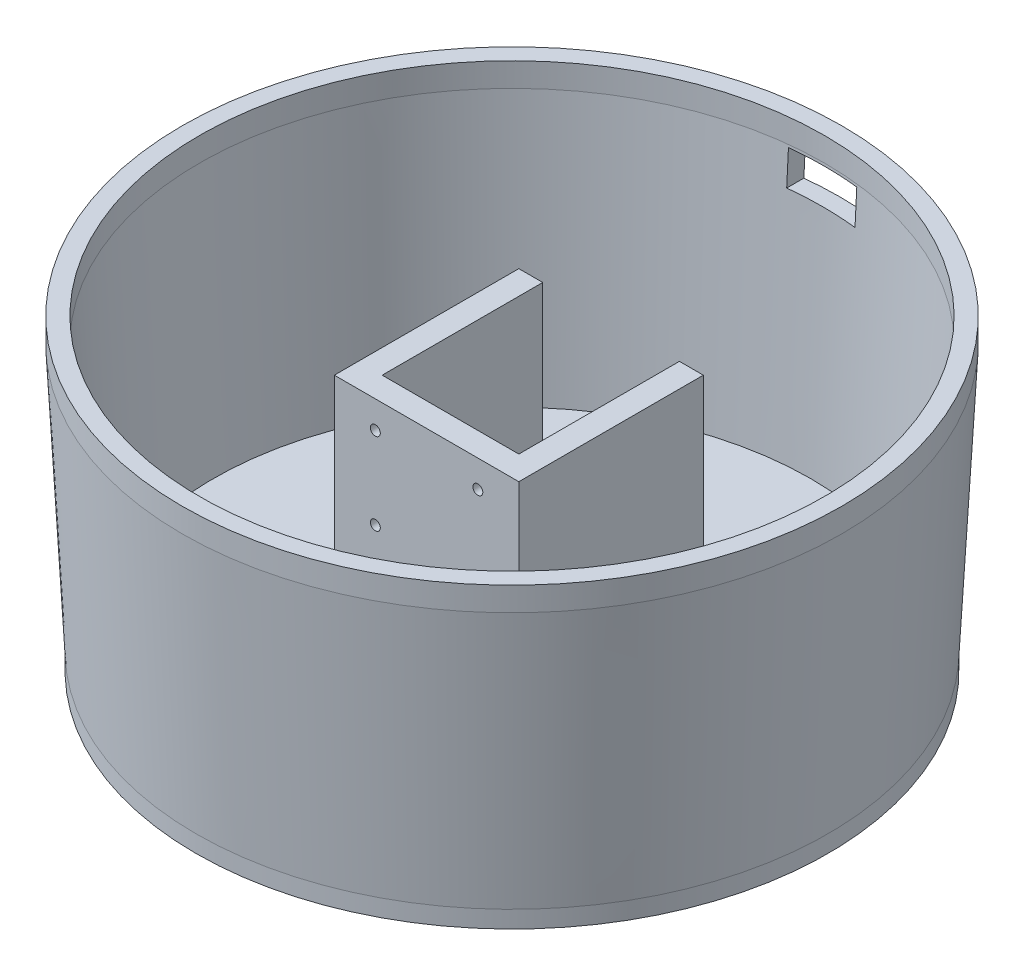
SolidWorks part; units mm, degrees
ref_plane "정면" through (0, 0, 0) normal (0, 0, 1) x (1, 0, 0)
ref_plane "윗면" through (0, 0, 0) normal (0, 1, 0) x (1, 0, 0)
ref_plane "우측면" through (0, 0, 0) normal (1, 0, 0) x (0, 0, -1)
sketch "스케치1" plane through (0, 0, 0) normal (0, 1, 0) x (1, 0, 0)
  circle A0 centre (0, 0) radius 92.5
  circle A1 centre (0, 0) radius 15.2
  dimension "D1" = 185
  dimension "D2" = 30.4
extrude "보스-돌출1" add sketch "스케치1" along normal blind 5
sketch "스케치5" plane through (0, 0, 0) normal (0, 0, 1) x (1, 0, 0)
  line L0 (-92.5, 5) -> (-96.5, 83)
  line L1 (-96.5, 83) -> (-91.5, 83)
  line L2 (-91.5, 83) -> (-87.5, 5)
  line L3 (92.5, 5) -> (-92.5, 5) construction
  line L4 (-87.5, 5) -> (-92.5, 5)
  line L5 (0, 0) -> (0, 65.4419) construction
  dimension "D1" = 5
  dimension "D2" = 78
  dimension "D3" = 91.5
revolve "회전1" add sketch "스케치5" angle 360 about L5
sketch "스케치8" plane through (0, 0, 0) normal (0, 0, 1) x (1, 0, 0)
  line L0 (-96.5, 83) -> (-96.5, 90)
  line L1 (-96.5, 83) -> (-91.5, 83)
  line L2 (-91.5, 83) -> (-91.5, 90)
  line L3 (-91.5, 90) -> (-96.5, 90)
  line L4 (0, 0) -> (0, 88.409) construction
  dimension "D1" = 7
revolve "회전3" add sketch "스케치8" angle 360 about L4
ref_plane "평면1" through (0, 52, 0) normal (0, 1, 0) x (1, 0, 0)
sketch "스케치9" plane through (0, 5, 0) normal (0, 1, 0) x (1, 0, 0)
  line L5 (-20, -25) -> (20, -25)
  line L7 (-20, -18) -> (20, -18)
  line L11 (-20, -25) -> (-27, -25)
  line L12 (-20, -18) -> (-20, 29)
  line L13 (-20, 29) -> (-27, 29)
  line L14 (-27, -25) -> (-27, 29)
  line L15 (20, -25) -> (27, -25)
  line L16 (20, -18) -> (20, 29)
  line L17 (20, 29) -> (27, 29)
  line L18 (27, -25) -> (27, 29)
  point P0 (0, -21.5)
  dimension "D1" = 18
  dimension "D2" = 7
  dimension "D3" = 40
  dimension "D4" = 7
  dimension "D5" = 7
  dimension "D6" = 54
  dimension "D7" = 54
extrude "보스-돌출2" add sketch "스케치9" along normal blind 85
sketch "스케치11" plane through (0, 0, 25) normal (0, 0, 1) x (1, 0, 0)
  line L0 (27, 90) -> (27, 5) construction
  line L1 (-27, 5) -> (27, 5) construction
  line L2 (0, 5) -> (0, 105.899) construction
  circle A0 centre (15, 42) radius 1.45
  circle A1 centre (-15, 42) radius 1.45
  circle A2 centre (-15, 66) radius 1.45
  circle A3 centre (15, 66) radius 1.45
  dimension "D3" = 2.9
  dimension "D4" = 2.9
  dimension "D1" = 12
  dimension "D2" = 37
  dimension "D5" = 24
extrude "컷-돌출1" cut sketch "스케치11" against normal blind 85
sketch "스케치12" plane through (0, 0, 25) normal (0, 0, 1) x (1, 0, 0)
  line L0 (27, 90) -> (27, 5) construction
  line L1 (-27, 90) -> (27, 90)
  line L2 (-27, 90) -> (-27, 74)
  line L3 (-27, 74) -> (27, 74)
  line L4 (27, 90) -> (27, 74)
  point P7 (-15, 66)
  dimension "D1" = 8
extrude "컷-돌출2" cut sketch "스케치12" against normal blind 85
sketch "스케치14" plane through (0, 0, 0) normal (0, 0, 1) x (1, 0, 0)
  line L1 (-10, 72.2289) -> (10, 72.2289)
  line L2 (-10, 72.2289) -> (-10, 82.2289)
  line L3 (-10, 82.2289) -> (10, 82.2289)
  line L4 (10, 72.2289) -> (10, 82.2289)
  line L5 (-10, 72.2289) -> (10, 82.2289) construction
  line L6 (-10, 82.2289) -> (10, 72.2289) construction
  point P0 (0, 77.2289)
  point P5 (0, 0)
  dimension "D1" = 20
  dimension "D2" = 10
extrude "컷-돌출3" cut sketch "스케치14" against normal blind 100
